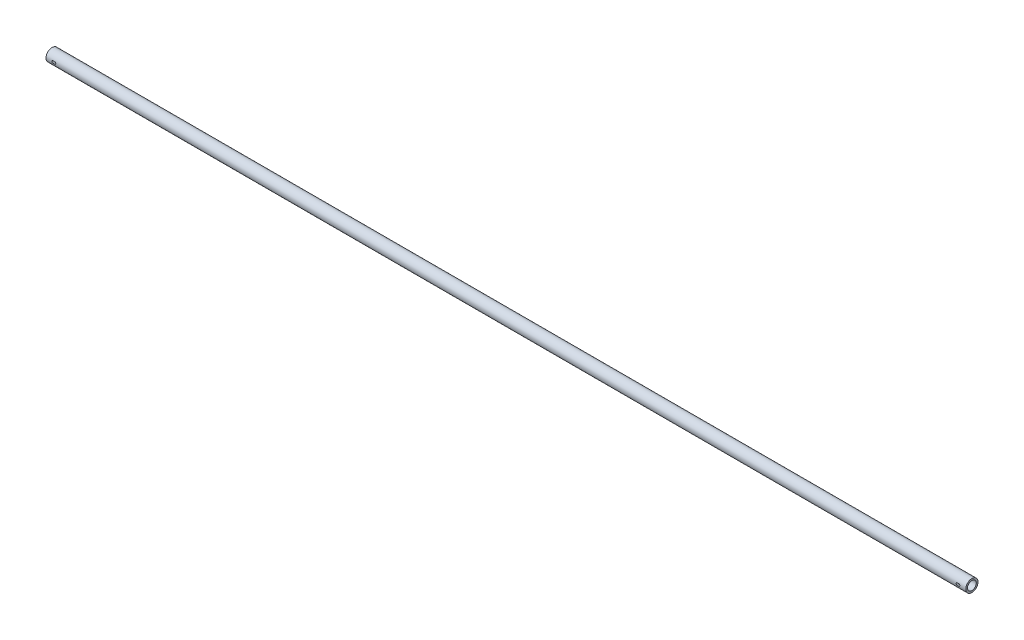
SolidWorks part; units mm, degrees
material "普通碳钢"
ref_plane "前视基准面" through (0, 0, 0) normal (0, 0, 1) x (1, 0, 0)
ref_plane "上视基准面" through (0, 0, 0) normal (0, 1, 0) x (1, 0, 0)
ref_plane "右视基准面" through (0, 0, 0) normal (1, 0, 0) x (0, 0, -1)
sketch "草图1" plane through (0, 0, 0) normal (1, 0, 0) x (0, 0, -1)
  circle A0 centre (0, 0) radius 17.5
  circle A1 centre (0, 0) radius 12
  dimension "D1" = 24
  dimension "D2" = 35
extrude "凸台-拉伸1" add sketch "草图1" along normal blind 2636
sketch "草图2" plane through (0, 0, 0) normal (-1, 0, 0) x (0, 0, 1)
  circle A0 centre (0, 0) radius 12.6
  dimension "D1" = 25.2
extrude "切除-拉伸1" cut sketch "草图2" against normal blind 52
sketch "草图3" plane through (2636, 0, 0) normal (1, 0, 0) x (0, 0, -1)
  circle A0 centre (0, 0) radius 12.6
  dimension "D1" = 25.2
extrude "切除-拉伸2" cut sketch "草图3" against normal blind 52
sketch "草图4" plane through (0, 0, 0) normal (0, 0, 1) x (1, 0, 0)
  line L0 (0, 0) -> (28, 0) construction
  line L1 (20, 3) -> (25, 3)
  line L2 (20, -3) -> (25, -3)
  arc A0 (20, 3) -> (20, -3) centre (20, 0) ccw
  arc A1 (25, -3) -> (25, 3) centre (25, 0) ccw
  dimension "D1" = 20
  dimension "D2" = 6
  dimension "D3" = 6
  dimension "D4" = 5
  dimension "D5" = 6
extrude "切除-拉伸3" cut sketch "草图4" against normal mid plane 40
sketch "草图5" plane through (0, 0, 0) normal (0, 0, 1) x (1, 0, 0)
  line L0 (2636, -17.5) -> (2636, 17.5) construction
  line L1 (2636, 0) -> (2611, 0) construction
  line L2 (2611, 3) -> (2616, 3)
  line L3 (2611, -3) -> (2616, -3)
  arc A0 (2616, -3) -> (2616, 3) centre (2616, 0) ccw
  arc A1 (2611, 3) -> (2611, -3) centre (2611, 0) ccw
  dimension "D1" = 20
  dimension "D2" = 6
  dimension "D3" = 6
  dimension "D4" = 5
extrude "切除-拉伸4" cut sketch "草图5" against normal mid plane 40
